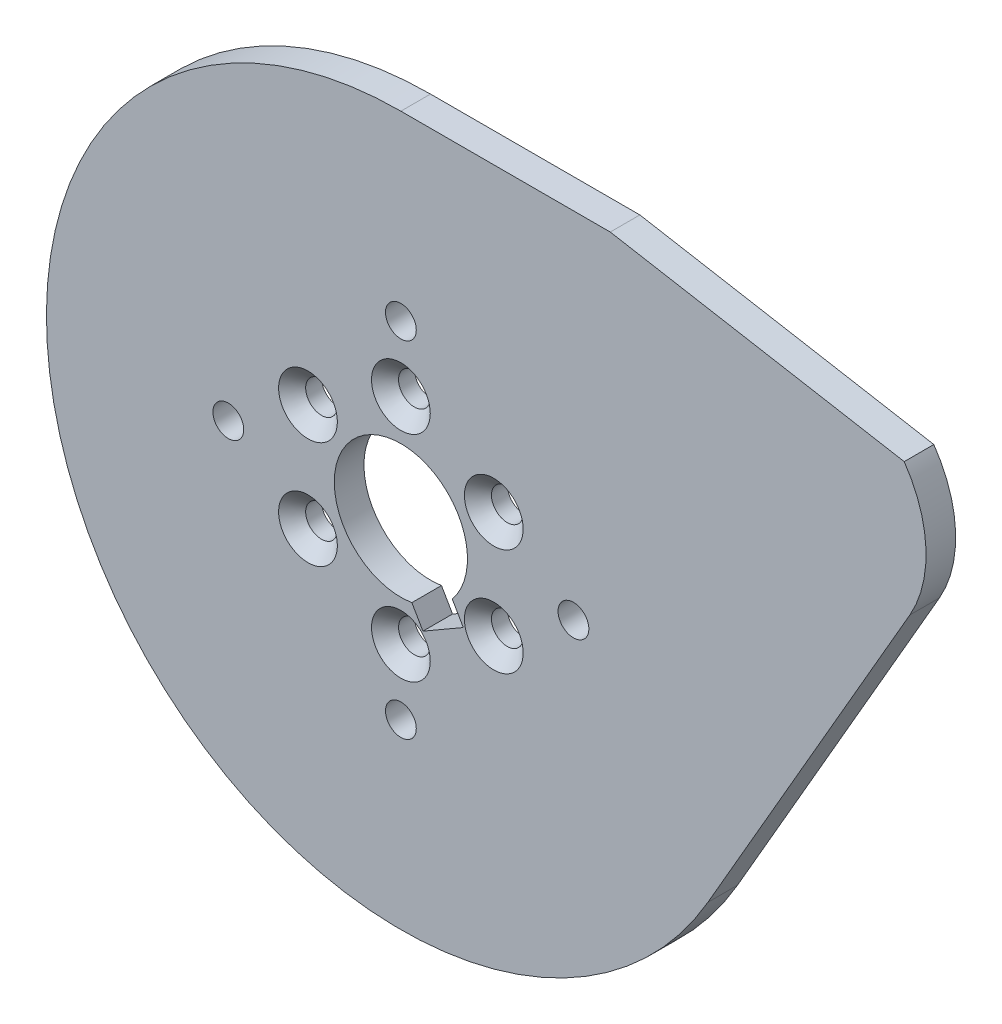
SolidWorks part; units mm, degrees
ref_plane "Front Plane" through (0, 0, 0) normal (0, 0, 1) x (1, 0, 0)
ref_plane "Top Plane" through (0, 0, 0) normal (0, 1, 0) x (1, 0, 0)
ref_plane "Right Plane" through (0, 0, 0) normal (1, 0, 0) x (0, 0, -1)
ref_plane "Plane1" through (0, 0, 3.175) normal (0, 0, 1) x (1, 0, 0)
sketch "Sketch1" plane through (0, 0, 3.175) normal (0, 0, 1) x (1, 0, 0)
  line L0 (32.909, -19) -> (54.5596, 18.5)
  line L1 (53.9595, 32.4433) -> (22.4457, 38)
  line L2 (22.4457, 38) -> (0, 38)
  arc A0 (0, 38) -> (32.909, -19) centre (0, 0) ccw
  arc A1 (54.5596, 18.5) -> (53.9595, 32.4433) centre (43.3013, 25) ccw
extrude "Boss-Extrude1" add sketch "Sketch1" against normal blind 3.175
sketch "Sketch2" plane through (0, 0, 0) normal (0, 0, -1) x (-1, 0, 0)
  line L0 (-5.5077, -4.5396) -> (-6.6943, -6.5949)
  line L1 (-6.6943, -6.5949) -> (-2.3642, -9.0949)
  line L2 (-2.3642, -9.0949) -> (-1.1776, -7.0396)
  arc A0 (-1.1776, -7.0396) -> (-5.5077, -4.5396) centre (0, 0) cw
extrude "Cut-Extrude1" cut sketch "Sketch2" against normal through all
ref_plane "Plane2" through (0, 0, 0) normal (0, -1, 0) x (1, 0, 0)
sketch "Sketch3" plane through (0, 0, 0) normal (0, -1, 0) x (1, 0, 0)
  line L0 (7.1374, 3.175) -> (0, 3.175)
  line L1 (0, 3.175) -> (0, 0)
  line L2 (0, 0) -> (7.1374, 0)
  line L3 (7.1374, 0) -> (7.1374, 3.175)
  line L4 (0, 3.175) -> (0, 0) construction
revolve "Cut-Revolve1" cut sketch "Sketch3" angle 360 about L4
hole_wizard "Ø3.3 (3.3) Diameter Hole1" positions "Sketch5" profile "Sketch4" hole size "Ø3.3" standard "ANSI Metric"
sketch "Sketch5" plane through (0, 0, 3.175) normal (0, 0, 1) x (1, 0, 0)
  point P0 (18.5, 0)
  point P1 (0, -18.5)
  point P2 (-18.5, 0)
  point P3 (0, 18.5)
sketch "Sketch4" plane through (18.5, 0, 3.175) normal (1, 0, 0) x (0, -1, 0)
  line L0 (0, 0) -> (0, 3.175)
  line L1 (0, 3.175) -> (1.65, 3.175)
  line L2 (1.65, 3.175) -> (1.65, 0)
  line L5 (1.65, 0) -> (0, 0)
  line L11 (0, -6.35) -> (0, 107.95) construction
  dimension "Thru Hole Dia." = 3.3
  dimension "Thru Hole Depth" = 3.175
hole_wizard "CSK for M3 Flat Head Machine Screw1" positions "Sketch7" profile "Sketch6" countersink size "M3" standard "ANSI Metric"
sketch "Sketch7" plane through (0, 0, 3.175) normal (0, 0, 1) x (1, 0, 0)
  point P0 (-9.9593, 5.75)
  point P1 (-9.9593, -5.75)
  point P2 (0, -11.5)
  point P3 (9.9593, -5.75)
  point P4 (9.9593, 5.75)
  point P5 (0, 11.5)
sketch "Sketch6" plane through (-9.9593, 5.75, 3.175) normal (1, 0, 0) x (0, -1, 0)
  line L0 (0, 0) -> (0, 3.175)
  line L1 (0, 3.175) -> (1.7, 3.175)
  line L2 (1.7, 3.175) -> (1.7, 1.45)
  line L3 (1.7, 1.45) -> (3.15, 0)
  line L5 (3.15, 0) -> (0, 0)
  line L6 (-1.7, 1.45) -> (-3.15, 0) construction
  line L11 (0, -6.35) -> (0, 107.95) construction
  dimension "Thru Hole Dia." = 3.4
  dimension "Thru Hole Depth" = 3.175
  dimension "Near C'Sink Dia." = 6.3
  dimension "Near C'Sink Angle" = 90
